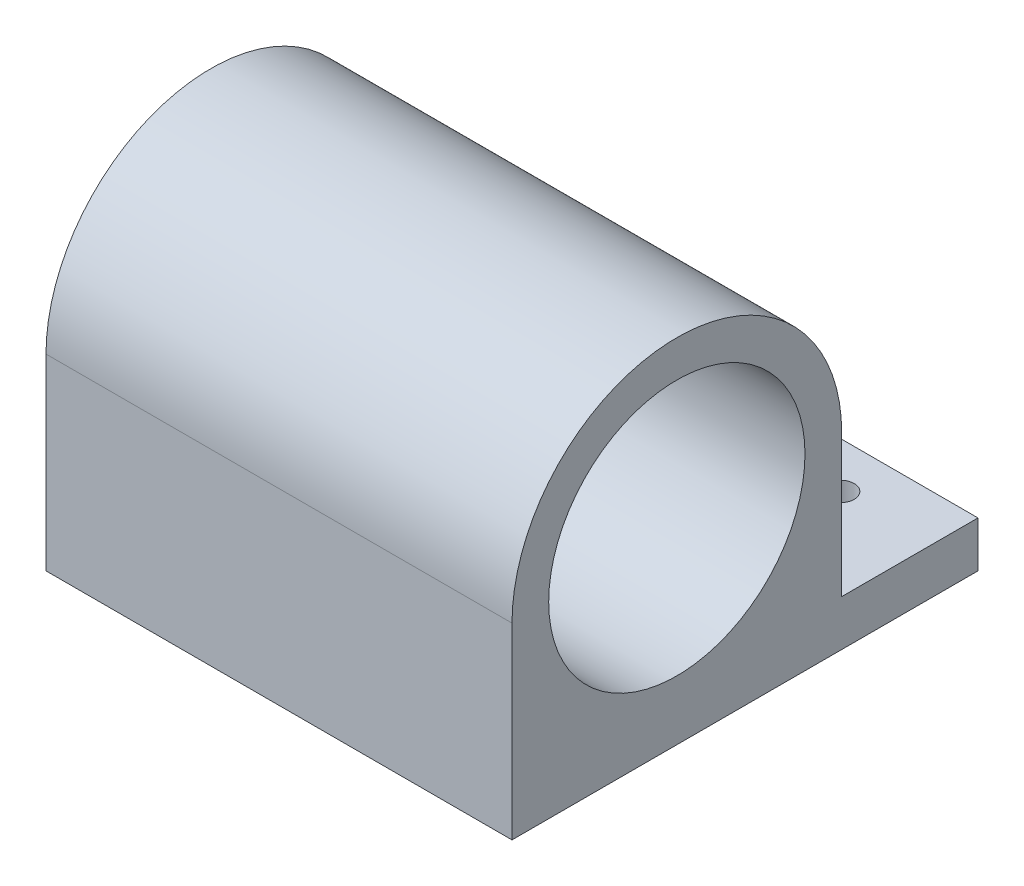
SolidWorks part; units mm, degrees
ref_plane "Front Plane" through (0, 0, 0) normal (0, 0, 1) x (1, 0, 0)
ref_plane "Top Plane" through (0, 0, 0) normal (0, 1, 0) x (1, 0, 0)
ref_plane "Right Plane" through (0, 0, 0) normal (1, 0, 0) x (0, 0, -1)
sketch "Sketch1" plane through (0, 0, 0) normal (0, 1, 0) x (1, 0, 0)
  line L0 (0, 45.8) -> (50.8, 45.8) construction
  line L1 (0, 0) -> (50.8, 0)
  line L2 (0, 0) -> (0, 50.8)
  line L3 (0, 50.8) -> (50.8, 50.8)
  line L4 (50.8, 0) -> (50.8, 50.8)
  circle A0 centre (10, 45.8) radius 1.5
  circle A1 centre (40.8, 45.8) radius 1.5
  point P11 (0, 0)
  point P12 (8.176, 32.4556)
  dimension "D3" = 3
  dimension "D4" = 3
  dimension "D1" = 50.8
  dimension "D2" = 50.8
  dimension "D5" = 10
  dimension "D6" = 10
  dimension "D7" = 5
extrude "Boss-Extrude1" add sketch "Sketch1" along normal blind 5
sketch "Sketch2" plane through (0, 0, 0) normal (-1, 0, 0) x (0, 0, 1)
  line L0 (-50.8, 2.5) -> (0, 2.5) construction
  line L1 (-50.8, 5) -> (-50.8, 0) construction
  line L2 (0, 5) -> (0, 0) construction
  line L3 (0, 2.5) -> (0, 34.4481) construction
  line L4 (-35.94, 20.47) -> (-35.94, 0)
  line L5 (-50.8, 0) -> (0, 0) construction
  line L6 (-35.94, 0) -> (0, 0)
  line L7 (0, 0) -> (0, 20.47)
  line L8 (0, 20.47) -> (-35.94, 20.47)
  circle A0 centre (-17.97, 20.47) radius 13.97
  circle A1 centre (-17.97, 20.47) radius 17.97
  line M7 (0, 5) -> (-50.8, 5)
  dimension "D1" = 27.94
  dimension "D2" = 4
extrude "Boss-Extrude2" add sketch "Sketch2" against normal up to surface (50.8 mm away) contours A1 L4 M7 | A1 L7 M7 | L8 A1 A0 M7 | L8 A1 A0 up to face at (50.8, 2.5, -25.4)
